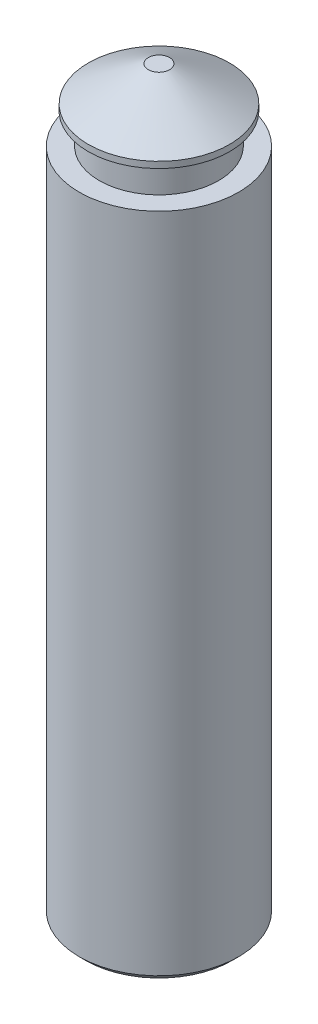
SolidWorks part; units mm, degrees
material "AISI 316 Stainless Steel Sheet (SS)"
ref_plane "Front Plane" through (0, 0, 0) normal (0, 0, 1) x (1, 0, 0)
ref_plane "Top Plane" through (0, 0, 0) normal (0, 1, 0) x (1, 0, 0)
ref_plane "Right Plane" through (0, 0, 0) normal (1, 0, 0) x (0, 0, -1)
sketch "Sketch1" plane through (0, 0, 0) normal (0, 1, 0) x (1, 0, 0)
  circle A0 centre (0, 0) radius 18.542
extrude "Boss-Extrude1" add sketch "Sketch1" along normal blind 155.575
sketch "Sketch2" plane through (0, 155.575, 0) normal (0, 1, 0) x (1, 0, 0)
  circle A0 centre (0, 0) radius 13.8811
extrude "Boss-Extrude2" add sketch "Sketch2" along normal blind 7.112
sketch "Sketch3" plane through (0, 162.687, 0) normal (0, 1, 0) x (1, 0, 0)
  circle A0 centre (0, 0) radius 16.4338
extrude "Boss-Extrude3" add sketch "Sketch3" along normal blind 9.525
chamfer "Chamfer1" distance 13.97 angle 30 1 edges at (0, 172.212, 16.4338)
chamfer "Chamfer2" distance 1.524 angle 45 1 edges at (0, 0, 18.542)
